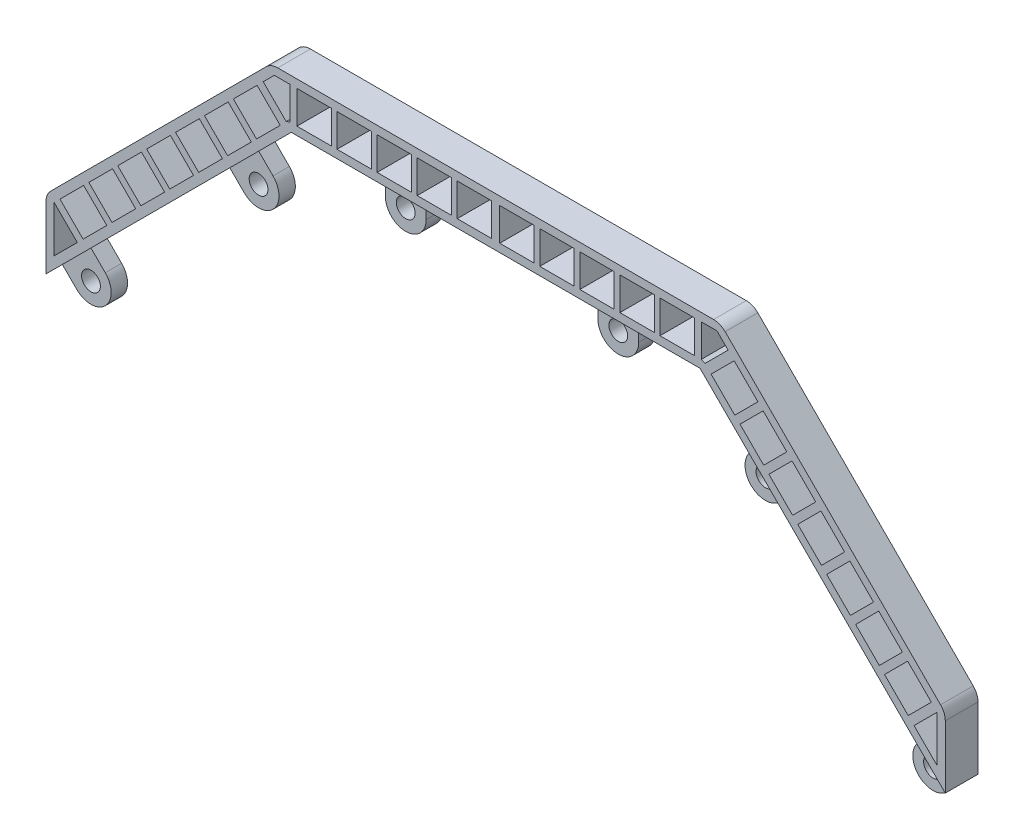
SolidWorks part; units mm, degrees
ref_plane "Front Plane" through (0, 0, 0) normal (0, 0, 1) x (1, 0, 0)
ref_plane "Top Plane" through (0, 0, 0) normal (0, 1, 0) x (1, 0, 0)
ref_plane "Right Plane" through (0, 0, 0) normal (1, 0, 0) x (0, 0, -1)
sketch "Sketch2" plane through (0, 0, 0) normal (0, 0, 1) x (1, 0, 0)
  line L0 (-55, 25) -> (-55, -25) construction
  line L1 (-55, -25) -> (-25, -55) construction
  line L2 (-25, -55) -> (25, -55) construction
  line L3 (25, -55) -> (55, -25) construction
  line L4 (55, -25) -> (55, 25) construction
  line L5 (55, 25) -> (25, 55) construction
  line L6 (25, 55) -> (-25, 55) construction
  line L7 (-25, 55) -> (-55, 25) construction
  point P7 (0, 55)
  point P9 (-55, 0)
  dimension "D1" = 50
  dimension "D2" = 30
  dimension "D3" = 30
  dimension "D4" = 30
sketch "Sketch3" plane through (0, 0, 0) normal (0, 0, 1) x (1, 0, 0)
  line L0 (-55, 25) -> (-53.25, 23.25)
  line L1 (-49.75, 26.75) -> (-51.5, 28.5)
  line L2 (-25, 55) -> (-55, 25) construction
  line L3 (-51.5, 28.5) -> (-34.5178, 45.4822)
  line L4 (-25, 55) -> (-15.5, 55)
  line L5 (25, 55) -> (-25, 55) construction
  line L6 (-15.5, 55) -> (-15.5, 52)
  line L7 (-10.5, 52) -> (-10.5, 55)
  line L8 (-10.5, 55) -> (0, 55)
  line L9 (0, 55) -> (0, 61)
  line L10 (0, 61) -> (-27.4853, 61)
  line L11 (-27.4853, 61) -> (-55, 33.4853)
  line L12 (-55, 33.4853) -> (-55, 25)
  line L13 (-34.5178, 45.4822) -> (-32.7678, 43.7322)
  line L14 (-29.2322, 47.2678) -> (-30.9822, 49.0178)
  line L15 (-30.9822, 49.0178) -> (-25, 55)
  arc A0 (-53.25, 23.25) -> (-49.75, 26.75) centre (-51.5, 25) ccw
  arc A1 (-15.5, 52) -> (-10.5, 52) centre (-13, 52) ccw
  arc A2 (-32.7678, 43.7322) -> (-29.2322, 47.2678) centre (-31, 45.5) ccw
  circle A3 centre (-13, 52) radius 1.15
  circle A4 centre (-31, 45.5) radius 1.15
  circle A5 centre (-51.5, 25) radius 1.15
  dimension "D2" = 2.5
  dimension "D8" = 2.5
  dimension "D10" = 2.4749
  dimension "D11" = 2.3
  dimension "D4" = 6
  dimension "D5" = 6
  dimension "D6" = 3
  dimension "D9" = 6
  dimension "D1" = 9.5
  dimension "D7" = 3.5
  dimension "D3" = 12
extrude "Boss-Extrude1" add sketch "Sketch3" along normal mid plane 4
sketch "Sketch8" plane through (0, 0, 2) normal (0, 0, 1) x (1, 0, 0)
  line L0 (-55, 25) -> (-51.5, 28.5)
  line L1 (-34.5178, 45.4822) -> (-30.9822, 49.0178)
  line L2 (-15.5, 55) -> (-10.5, 55)
  line L14 (-55, 33.4853) -> (-55, 25)
  line L15 (-55, 25) -> (-53.25, 23.25)
  line L16 (-49.75, 26.75) -> (-51.5, 28.5)
  line L17 (-51.5, 28.5) -> (-34.5178, 45.4822)
  line L18 (-34.5178, 45.4822) -> (-32.7678, 43.7322)
  line L19 (-29.2322, 47.2678) -> (-30.9822, 49.0178)
  line L20 (-30.9822, 49.0178) -> (-25, 55)
  line L21 (-25, 55) -> (-15.5, 55)
  line L22 (-15.5, 55) -> (-15.5, 52)
  line L23 (-10.5, 52) -> (-10.5, 55)
  line L24 (-10.5, 55) -> (0, 55)
  line L25 (0, 55) -> (0, 61)
  line L26 (0, 61) -> (-27.4853, 61)
  line L27 (-27.4853, 61) -> (-55, 33.4853)
  line L29 (-55, 25) -> (-53.25, 23.25)
  line L30 (-49.75, 26.75) -> (-51.5, 28.5)
  line L32 (-34.5178, 45.4822) -> (-32.7678, 43.7322)
  line L33 (-29.2322, 47.2678) -> (-30.9822, 49.0178)
  line L36 (-15.5, 55) -> (-15.5, 52)
  line L37 (-10.5, 52) -> (-10.5, 55)
  arc A3 (-53.25, 23.25) -> (-49.75, 26.75) centre (-51.5, 25) ccw
  arc A4 (-32.7678, 43.7322) -> (-29.2322, 47.2678) centre (-31, 45.5) ccw
  arc A5 (-15.5, 52) -> (-10.5, 52) centre (-13, 52) ccw
  arc A6 (-53.25, 23.25) -> (-49.75, 26.75) centre (-51.5, 25) ccw
  arc A7 (-32.7678, 43.7322) -> (-29.2322, 47.2678) centre (-31, 45.5) ccw
  arc A8 (-15.5, 52) -> (-10.5, 52) centre (-13, 52) ccw
  dimension "D1" = 0
extrude "Cut-Extrude4" cut sketch "Sketch8" against normal blind 2
fillet "Fillet1" radius 2 2 edges at (-55, 33.4853, 0) (-27.4853, 61, 0)
sketch "Sketch5" plane through (0, 0, 2) normal (0, 0, 1) x (1, 0, 0)
  line L0 (-28.4283, 58.6428) -> (-27.0711, 60)
  line L1 (-27.0711, 60) -> (-25.1517, 60)
  line L2 (-25.1517, 60) -> (-25.1517, 56.0196)
  line L3 (-25.1517, 56.0196) -> (-25.6137, 55.8282)
  line L4 (-25.6137, 55.8282) -> (-28.4283, 58.6428)
  line L5 (-54, 33.0711) -> (-54, 27.4142)
  line L6 (-54, 27.4142) -> (-51.1716, 30.2426)
  line L7 (-51.1716, 30.2426) -> (-54, 33.0711)
  line L8 (-25, 55) -> (-55, 25) construction
  line L9 (25, 55) -> (-25, 55) construction
  line L10 (0, 61) -> (-26.6569, 61) construction
  line L11 (-28.0711, 60.4142) -> (-54.4142, 34.0711) construction
  line L12 (-55, 32.6569) -> (-55, 25) construction
  circle A0 centre (-25, 55) radius 1 construction
  dimension "D1" = 2
  dimension "D2" = 1
  dimension "D3" = 1
  dimension "D4" = 0.5
  dimension "D5" = 1
  dimension "D6" = 1
  dimension "D7" = 1
extrude "Cut-Extrude1" cut sketch "Sketch5" against normal through all
sketch "Sketch6" plane through (0, 0, 0) normal (0, 0, 1) x (1, 0, 0)
  line L0 (-53.2929, 33.7782) -> (-50.3938, 36.6773)
  line L1 (-50.3938, 36.6773) -> (-47.5653, 33.8489)
  line L2 (-47.5653, 33.8489) -> (-50.4645, 30.9497)
  line L3 (-50.4645, 30.9497) -> (-53.2929, 33.7782)
  line L4 (-25, 55) -> (-55, 25) construction
  line L5 (-28.0711, 60.4142) -> (-54.4142, 34.0711) construction
  line L7 (-51.1716, 30.2426) -> (-54, 33.0711) construction
  dimension "D2" = 1
  dimension "D3" = 1
  dimension "D1" = 1
  dimension "D4" = 4.1
extrude "Cut-Extrude2" cut sketch "Sketch6" against normal through all both and the other way through all
pattern_linear "LPattern1" count 7 spacing 5 along (0.7071, 0.7071, 0) of "Cut-Extrude2"
sketch "Sketch7" plane through (0, 0, 0) normal (0, 0, 1) x (1, 0, 0)
  line L0 (0, 61) -> (-26.6569, 61) construction
  line L1 (-4.7, 60) -> (-0.5, 60)
  line L2 (-4.7, 60) -> (-4.7, 56)
  line L3 (-4.7, 56) -> (-0.5, 56)
  line L4 (-0.5, 60) -> (-0.5, 56)
  line L5 (-25, 55) -> (0, 55) construction
  line L6 (0, 55) -> (0, 61) construction
  dimension "D2" = 1
  dimension "D4" = 0.5
  dimension "D1" = 1
  dimension "D3" = 4.2
extrude "Cut-Extrude3" cut sketch "Sketch7" against normal through all both and the other way through all
pattern_linear "LPattern2" count 5 spacing 4.9 along (-1, 0, 0) of "Cut-Extrude3"
mirror "Mirror1" about plane through (0, 55, 2) normal (-1, 0, 0) of "Cut-Extrude4", "Boss-Extrude1", "LPattern2", "Cut-Extrude3", "LPattern1", "Cut-Extrude2", "Cut-Extrude1", "Fillet1"
equation "\"D5@Sketch3\"=\"D4@Sketch3\""
equation "\"D8@Sketch3\"=\"D2@Sketch3\""
equation "\"D3@Sketch5\"=\"ridge\""
equation "\"D1@Sketch5\"=2 * \"ridge\""
equation "\"ridge\"= 1"
equation "\"D2@Sketch5\"= \"ridge\""
equation "\"D5@Sketch5\"= \"ridge\""
equation "\"D6@Sketch5\"= \"ridge\""
equation "\"D7@Sketch5\"=\"ridge\""
equation "\"D1@Sketch6\"=\"ridge\""
equation "\"D2@Sketch6\"=\"ridge\""
equation "\"D1@Sketch7\"=\"ridge\""
equation "\"D2@Sketch7\"=\"ridge\""
